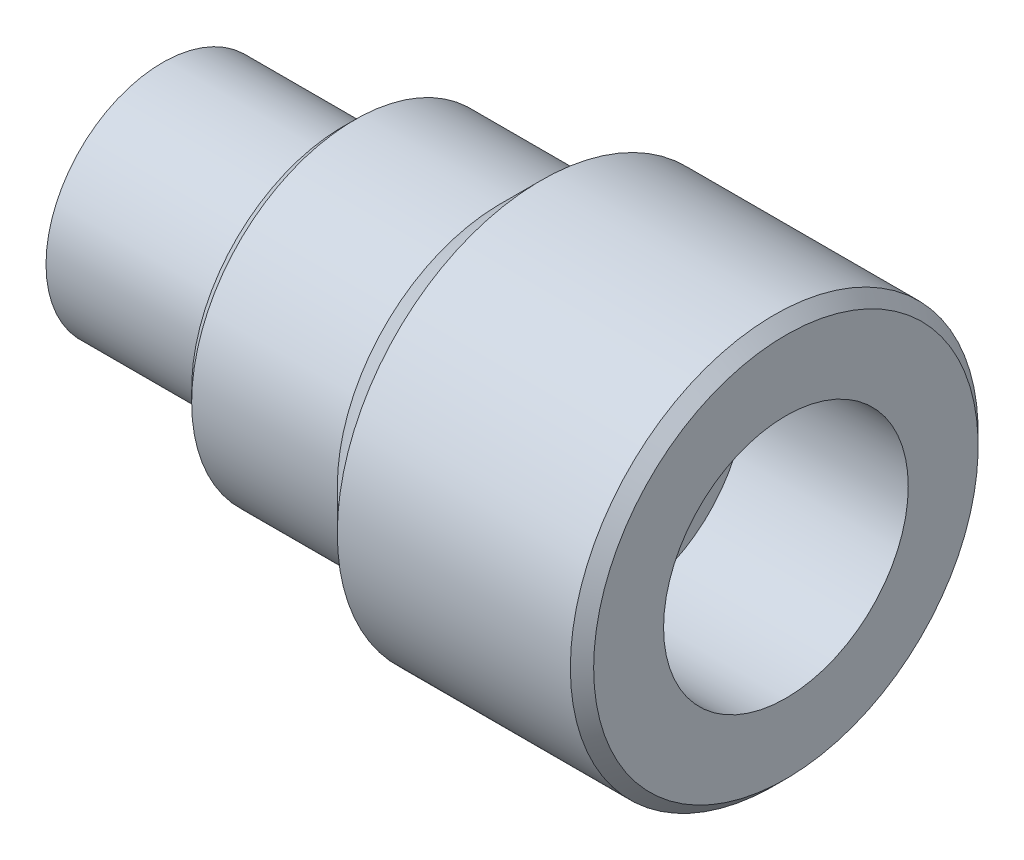
SolidWorks part; units mm, degrees
ref_plane "Front Plane" through (0, 0, 0) normal (0, 0, 1) x (1, 0, 0)
ref_plane "Top Plane" through (0, 0, 0) normal (0, 1, 0) x (1, 0, 0)
ref_plane "Right Plane" through (0, 0, 0) normal (1, 0, 0) x (0, 0, -1)
sketch "Sketch1" plane through (0, 0, 0) normal (0, 0, 1) x (1, 0, 0)
  line L0 (0, 0) -> (18.9142, 0) construction
  line L1 (0, 10) -> (0, 14)
  line L2 (0, 14) -> (13.5, 14)
  line L3 (13.5, 14) -> (17, 17.5)
  line L4 (17, 17.5) -> (38, 17.5)
  line L5 (38, 17.5) -> (38, 10.5)
  line L6 (38, 10.5) -> (24, 10.5)
  line L7 (24, 10.5) -> (24, 6)
  line L8 (24, 6) -> (14.5, 6)
  line L9 (14.5, 6) -> (14.5, 10)
  line L10 (14.5, 10) -> (0, 10)
  dimension "D1" = 10
  dimension "D2" = 10.5
  dimension "D3" = 4
  dimension "D4" = 14.5
  dimension "D5" = 14
  dimension "D6" = 38
  dimension "D7" = 4
  dimension "D8" = 135
  dimension "D9" = 1
  dimension "D10" = 7
revolve "Revolve1" add sketch "Sketch1" angle 360 about L0
chamfer "Chamfer1" distance 1 angle 45 2 edges at (38, 0, 17.5) (0, 0, 14)
sketch "Sketch2" plane through (14.5, 0, 0) normal (-1, 0, 0) x (0, 0, 1)
  circle A0 centre (0, 0) radius 6 construction
  circle A1 centre (0, 0) radius 10
  circle A2 centre (0, 0) radius 10
  circle A3 centre (0, 0) radius 6
  dimension "D1" = 0
extrude "Boss-Extrude1" add sketch "Sketch2" along normal blind 30 separate body
